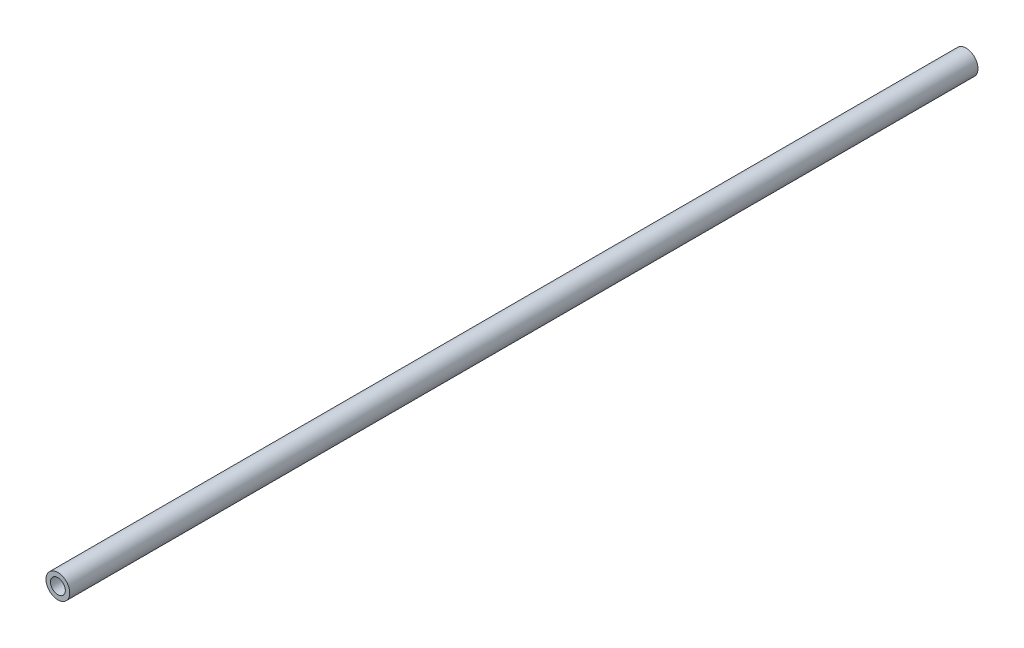
SolidWorks part; units mm, degrees
material "AISI 304"
ref_plane "Front Plane" through (0, 0, 0) normal (0, 0, 1) x (1, 0, 0)
ref_plane "Top Plane" through (0, 0, 0) normal (0, 1, 0) x (1, 0, 0)
ref_plane "Right Plane" through (0, 0, 0) normal (1, 0, 0) x (0, 0, -1)
sketch "Sketch1" plane through (0, 0, 0) normal (0, 0, 1) x (1, 0, 0)
  circle A0 centre (0, 0) radius 8.55
  circle A1 centre (0, 0) radius 5.35
  dimension "D1" = 10.7
  dimension "D2" = 17.1
extrude "Boss-Extrude1" add sketch "Sketch1" against normal blind 653.17
